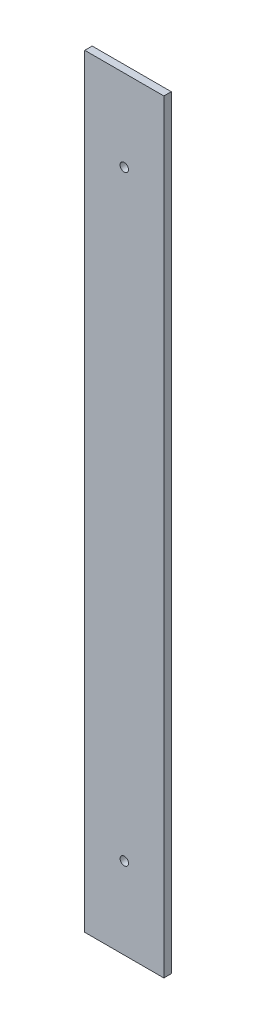
SolidWorks part; units mm, degrees
ref_plane "Plan de face" through (0, 0, 0) normal (0, 0, 1) x (1, 0, 0)
ref_plane "Plan de dessus" through (0, 0, 0) normal (0, 1, 0) x (1, 0, 0)
ref_plane "Plan de droite" through (0, 0, 0) normal (1, 0, 0) x (0, 0, -1)
sketch "Esquisse1" plane through (0, 0, 0) normal (0, 0, 1) x (1, 0, 0)
  line L1 (16, 154.5) -> (-16, 154.5)
  line L2 (16, 154.5) -> (16, -154.5)
  line L3 (16, -154.5) -> (-16, -154.5)
  line L4 (-16, 154.5) -> (-16, -154.5)
  line L5 (16, 154.5) -> (-16, -154.5) construction
  line L6 (16, -154.5) -> (-16, 154.5) construction
  point P0 (0, 0)
  dimension "D1" = 309
  dimension "D2" = 32
extrude "Boss.-Extru.1" add sketch "Esquisse1" along normal blind 3
sketch "Esquisse2" plane through (0, 0, 3) normal (0, 0, 1) x (1, 0, 0)
  line L0 (-16, 0) -> (16, 0) construction
  line L1 (-16, 154.5) -> (-16, -154.5) construction
  line L2 (16, -154.5) -> (16, 154.5) construction
  line L3 (0, 154.5) -> (0, 121.5) construction
  line L4 (16, 154.5) -> (-16, 154.5) construction
  circle A0 centre (0, 121.5) radius 1.7
  circle A1 centre (0, -121.5) radius 1.7
  dimension "D3" = 3.4
  dimension "D1" = 33
  dimension "D2" = 16
extrude "Enlèv. mat.-Extru.1" cut sketch "Esquisse2" against normal through all
